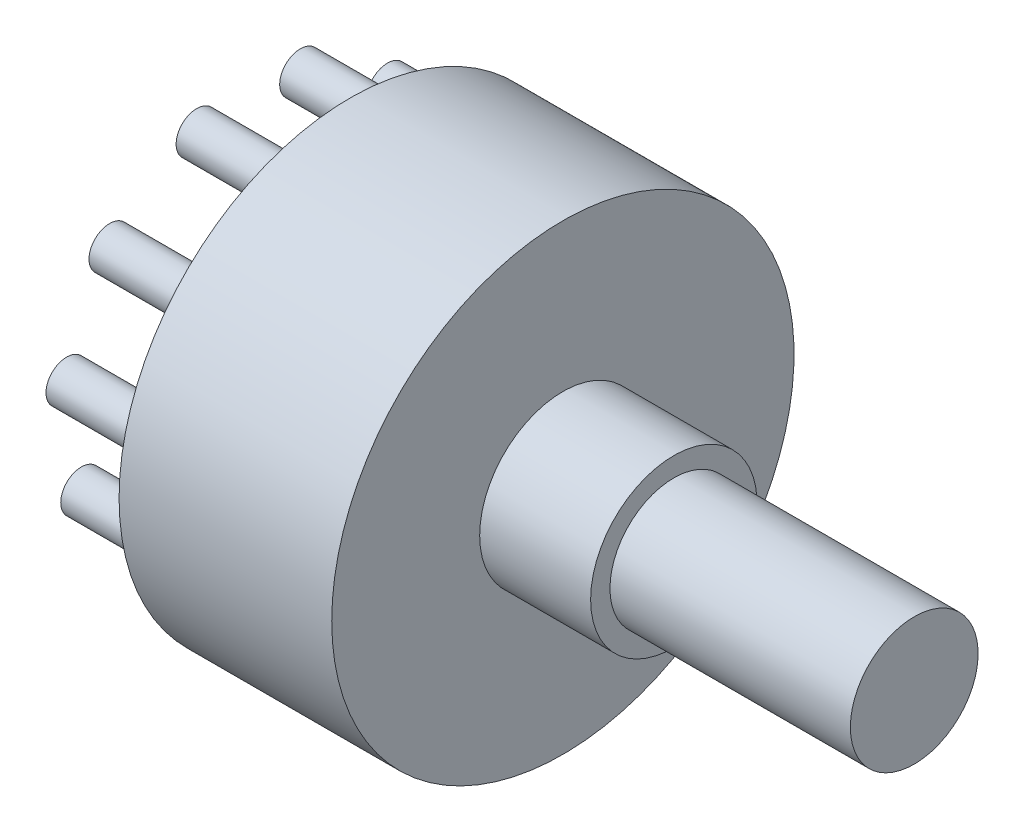
SolidWorks part; units mm, degrees
ref_plane "Płaszczyzna przednia" through (0, 0, 0) normal (0, 0, 1) x (1, 0, 0)
ref_plane "Płaszczyzna górna" through (0, 0, 0) normal (0, 1, 0) x (1, 0, 0)
ref_plane "Płaszczyzna prawa" through (0, 0, 0) normal (1, 0, 0) x (0, 0, -1)
sketch "Szkic1" plane through (0, 0, 0) normal (0, 0, 1) x (1, 0, 0)
  line L1 (17, 0) -> (7, 0)
  line L2 (5.5, 2.8292) -> (5.5, 4.8298)
  line L3 (17, 0) -> (17, 8)
  line L4 (17, 8) -> (23, 8)
  line L5 (23, 8) -> (23, 9.0456)
  line L6 (23, 9.0456) -> (36, 9.0456)
  line L9 (36, 12.5) -> (36, 9.0456)
  line L10 (7, 0) -> (5.5, 0)
  line L11 (5.5, 0) -> (5.5, 2.8292)
  line L16 (5.5, 4.8298) -> (5.5, 7.2379)
  line L17 (5.5, 9.0456) -> (5.5, 11.0582)
  line L19 (5.5, 11.0582) -> (5.5, 12.5)
  line L23 (5.5, 7.2379) -> (5.5, 9.0456)
  line L24 (5.5, 12.5) -> (36, 12.5)
  dimension "D2" = 10
  dimension "D4" = 8
  dimension "D5" = 6
  dimension "D6" = 13
revolve "Obrót2" add sketch "Szkic1" angle 360 about L24
sketch "Szkic3" plane through (5.5, 0, 0) normal (-1, 0, 0) x (0, 0, 1)
  line L0 (0, 0) -> (0, 25)
  line L1 (12.5, 12.5) -> (-12.5, 12.5)
  circle A0 centre (0, 12.5) radius 12.5 construction
  circle A1 centre (0, 2.5624) radius 1.1148
  circle A2 centre (5.3727, 4.1399) radius 1.1148
  circle A3 centre (9.0396, 8.3718) radius 1.1148
  circle A4 centre (9.8365, 13.9143) radius 1.1148
  circle A5 centre (7.5104, 19.0078) radius 1.1148
  circle A6 centre (2.7998, 22.0351) radius 1.1148
  circle A7 centre (-2.7998, 22.0351) radius 1.1148
  circle A8 centre (-7.5104, 19.0078) radius 1.1148
  circle A9 centre (-9.8365, 13.9143) radius 1.1148
  circle A10 centre (-9.0396, 8.3718) radius 1.1148
  circle A11 centre (-5.3727, 4.1399) radius 1.1148
  point P10 (0, 12.5)
  point P33 (0, 12.5)
  dimension "D1" = 11
extrude "Dodanie-wyciągnięcie1" add sketch "Szkic3" along normal blind 5.5 contours A11 | A2 | A3 | A4 | A5 | A7 | A8 | A9 | A10 | A1 | A6
